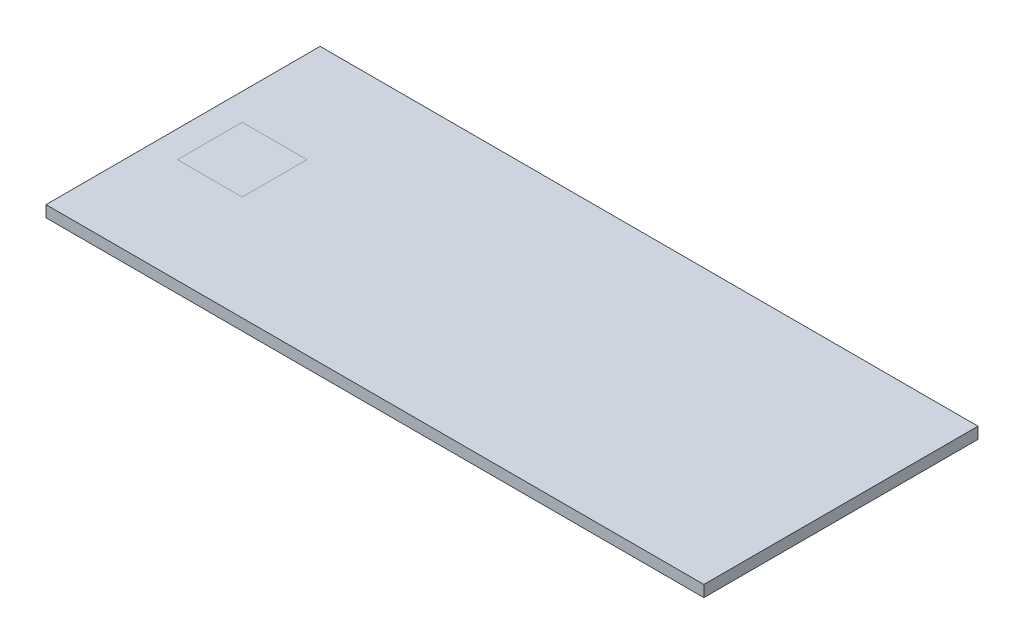
SolidWorks part; units mm, degrees
material "1023 Carbon Steel Sheet (SS)"
ref_plane "Front Plane" through (0, 0, 0) normal (0, 0, 1) x (1, 0, 0)
ref_plane "Top Plane" through (0, 0, 0) normal (0, 1, 0) x (1, 0, 0)
ref_plane "Right Plane" through (0, 0, 0) normal (1, 0, 0) x (0, 0, -1)
sketch "Sketch1" plane through (0, 0, 0) normal (1, 0, 0) x (0, 0, -1)
  line L0 (0, -1534.4769) -> (0, 75189.3682) construction
  line L1 (-381, 0) -> (381, 0)
  line L2 (381, 0) -> (381, -31.75)
  line L3 (381, -31.75) -> (349.25, -31.75)
  line L4 (-381, -31.75) -> (-349.25, -31.75)
  line L5 (-381, 0) -> (-381, -31.75)
  line L6 (-376.428, -27.178) -> (-349.25, -27.178)
  line L7 (-376.428, -4.572) -> (-376.428, -27.178)
  line L8 (-376.428, -4.572) -> (376.428, -4.572)
  line L9 (376.428, -4.572) -> (376.428, -27.178)
  line L10 (376.428, -27.178) -> (349.25, -27.178)
  line L11 (-349.25, -27.178) -> (-349.25, -31.75)
  line L12 (349.25, -27.178) -> (349.25, -31.75)
  point P10 (0, 0)
  dimension "D1" = 31.75
  dimension "D2" = 31.75
  dimension "D3" = 762
  dimension "D4" = 4.572
extrude "Boss-Extrude1" add sketch "Sketch1" along normal mid plane 1828.8
sketch "Sketch2" plane through (0, 0, 0) normal (0, 0, 1) x (1, 0, 0)
  line L0 (0, -1000) -> (0, 49000) construction
  line L1 (-914.4, 0) -> (-914.4, -31.75)
  line L2 (-914.4, -31.75) -> (-882.65, -31.75)
  line L3 (914.4, -31.75) -> (-914.4, -31.75) construction
  line L4 (-882.65, -31.75) -> (-882.65, -27.178)
  line L5 (-882.65, -27.178) -> (-909.828, -27.178)
  line L6 (-909.828, -27.178) -> (-909.828, 0)
  line L7 (914.4, 0) -> (-914.4, 0) construction
  line L8 (-909.828, 0) -> (-914.4, 0)
  line L9 (909.828, 0) -> (914.4, 0)
  line L10 (909.828, -27.178) -> (909.828, 0)
  line L11 (882.65, -27.178) -> (909.828, -27.178)
  line L12 (882.65, -31.75) -> (882.65, -27.178)
  line L13 (914.4, -31.75) -> (882.65, -31.75)
  line L14 (914.4, 0) -> (914.4, -31.75)
  dimension "D1" = 4.572
extrude "Boss-Extrude2" add sketch "Sketch2" along normal mid plane 762
sketch "Sketch3" plane through (0, 0, 0) normal (0, 1, 0) x (1, 0, 0)
  line L1 (-840, 90) -> (-660, 90)
  line L2 (-840, 90) -> (-840, -90)
  line L3 (-840, -90) -> (-660, -90)
  line L4 (-660, 90) -> (-660, -90)
  line L5 (-750, -90) -> (-750, 90) construction
  line L6 (-840, 0) -> (-660, 0) construction
  point P0 (-750, 0)
  dimension "D1" = 180
  dimension "D2" = 750
split line "Split Line1"
